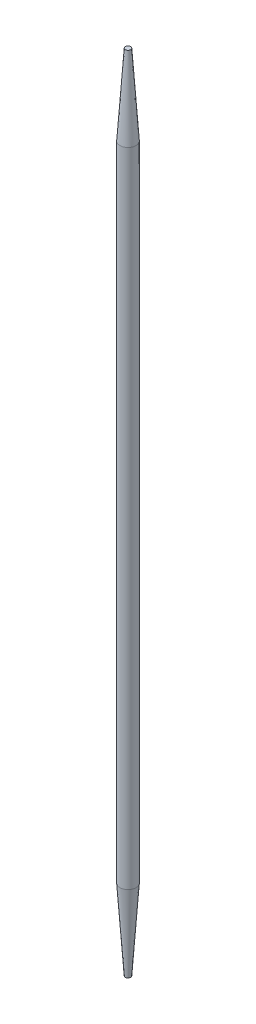
SolidWorks part; units mm, degrees
ref_plane "Plan de face" through (0, 0, 0) normal (0, 0, 1) x (1, 0, 0)
ref_plane "Plan de dessus" through (0, 0, 0) normal (0, 1, 0) x (1, 0, 0)
ref_plane "Plan de droite" through (0, 0, 0) normal (1, 0, 0) x (0, 0, -1)
sketch "Esquisse1" plane through (0, 0, 0) normal (0, 1, 0) x (1, 0, 0)
  circle A0 centre (0, 0) radius 1.5
  dimension "D1" = 3
extrude "Boss.-Extru.1" add sketch "Esquisse1" along normal blind 150
chamfer "Chanfrein1" distance 1 distance2 15 2 edges at (0, 150, 1.5) (0, 0, 1.5)
